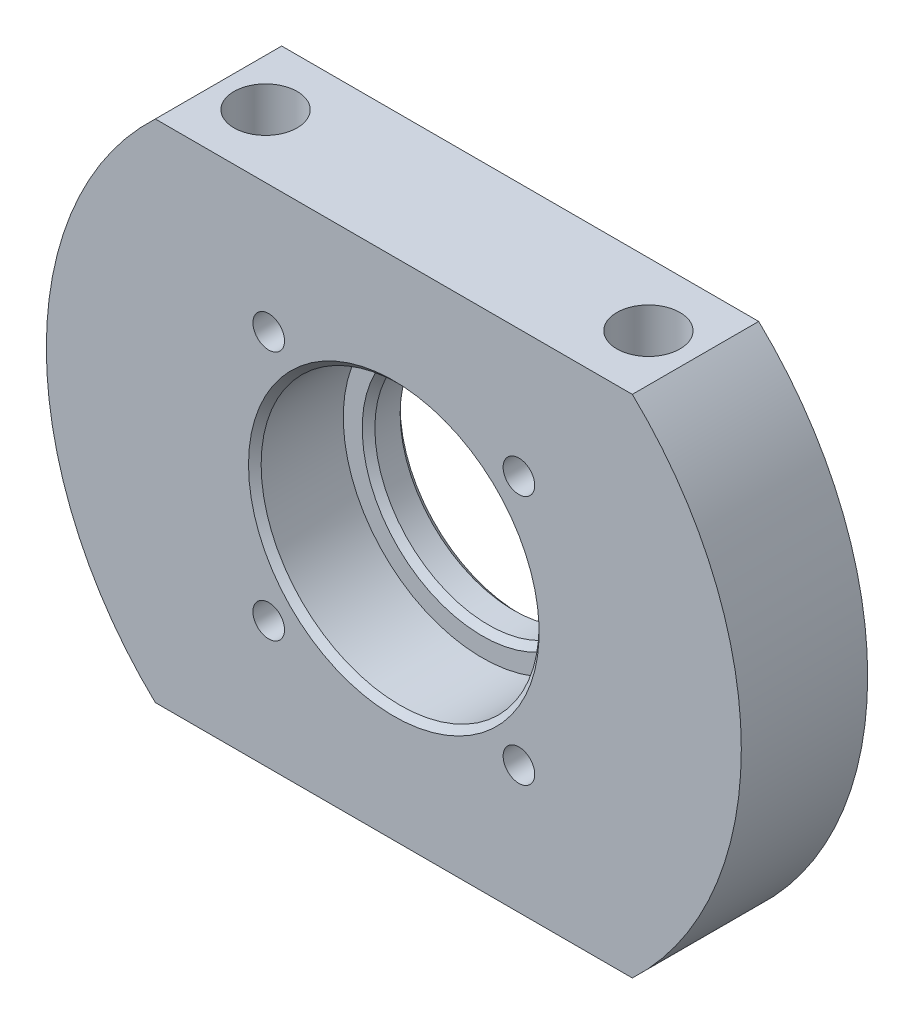
SolidWorks part; units mm, degrees
ref_plane "Face" through (0, 0, 0) normal (0, 0, 1) x (1, 0, 0)
ref_plane "Dessus" through (0, 0, 0) normal (0, 1, 0) x (1, 0, 0)
ref_plane "Droite" through (0, 0, 0) normal (1, 0, 0) x (0, 0, -1)
sketch "Esquisse1" plane through (0, 0, 0) normal (0, 0, 1) x (1, 0, 0)
  line L0 (0, 0) -> (37.7492, 0)
  line L1 (0, 40) -> (37.7492, 40)
  line L2 (18.8746, 0) -> (18.8746, 40) construction
  arc A0 (0, 0) -> (0, 40) centre (18.8746, 20) cw
  arc A1 (37.7492, 0) -> (37.7492, 40) centre (18.8746, 20) ccw
  circle A2 centre (18.8746, 20) radius 9
  dimension "D2" = 18
  dimension "D3" = 27.5
  dimension "D1" = 40
extrude "Extrusion1" add sketch "Esquisse1" along normal blind 10
sketch "Esquisse2" plane through (0, 0, 10) normal (0, 0, 1) x (1, 0, 0)
  circle A0 centre (18.8746, 20) radius 11
  dimension "D1" = 22
extrude "Enlèv. mat.-Extru.1" cut sketch "Esquisse2" against normal blind 7
chamfer "Chanfrein1" distance 0.5 angle 45 3 edges at (29.8746, 20, 10) (27.8746, 20, 3) (27.8746, 20, 0)
hole_wizard "Trou taraudé M31" positions "Esquisse4" profile "Esquisse3" tap size "M3" standard "ISO" end condition up to next
sketch "Esquisse4" plane through (0, 0, 10) normal (0, 0, 1) x (1, 0, 0)
  line L0 (18.8746, 40) -> (18.8746, 0) construction
  line L1 (37.7492, 40) -> (0, 40) construction
  line L2 (0, 0) -> (37.7492, 0) construction
  line L4 (8.9751, 29.8995) -> (28.7741, 10.1005) construction
  line L6 (8.9751, 10.1005) -> (28.7741, 29.8995) construction
  circle A0 centre (18.8746, 20) radius 14
  point P0 (28.7741, 29.8995)
  point P22 (8.9751, 29.8995)
  point P24 (8.9751, 10.1005)
  point P26 (28.7741, 10.1005)
  dimension "D1" = 28
  dimension "D2" = 45
  dimension "D3" = 45
sketch "Esquisse3" plane through (28.7741, 29.8995, 10) normal (1, 0, 0) x (0, -1, 0)
  line L0 (0, 0) -> (0, 10)
  line L1 (0, 10) -> (1.25, 10)
  line L2 (1.25, 10) -> (1.25, 0)
  line L5 (1.25, 0) -> (0, 0)
  line L11 (0, -6.35) -> (0, 107.95) construction
  dimension "Diamètre du trou pour taraudage jusqu'au prochain" = 2.5
  dimension "Profondeur du trou pour taraudage jusqu'au prochain" = 10
cosmetic thread "Filetage de perçage1" parameters "D2"=3
cosmetic thread "Filetage de perçage2" parameters "D2"=3
cosmetic thread "Filetage de perçage3" parameters "D2"=3
cosmetic thread "Filetage de perçage4" parameters "D2"=3
sketch "Esquisse6" plane through (0, 0, 0) normal (0, 0, -1) x (-1, 0, 0)
  line L0 (-7.7251, 29.8995) -> (-7.7251, 40) construction
  line L1 (-37.7492, 40) -> (0, 40) construction
  circle A0 centre (-8.9751, 29.8995) radius 1.25 construction
sketch "Esquisse7" plane through (0, 40, 0) normal (0, 1, 0) x (1, 0, 0)
  line L0 (0, -5) -> (37.7492, -5) construction
  line L1 (0, -10) -> (0, 0) construction
  line L2 (37.7492, -10) -> (37.7492, 0) construction
  line L3 (18.8746, 0) -> (18.8746, -10) construction
  line L4 (37.7492, 0) -> (0, 0) construction
  line L5 (37.7492, -10) -> (0, -10) construction
  line L6 (7.7251, 0) -> (7.7251, -10) construction
  circle A0 centre (3.7251, -5) radius 2.5
  circle A1 centre (34.0241, -5) radius 2.5
  dimension "D1" = 5
  dimension "D2" = 4
extrude "Enlèv. mat.-Extru.2" cut sketch "Esquisse7" against normal through all
